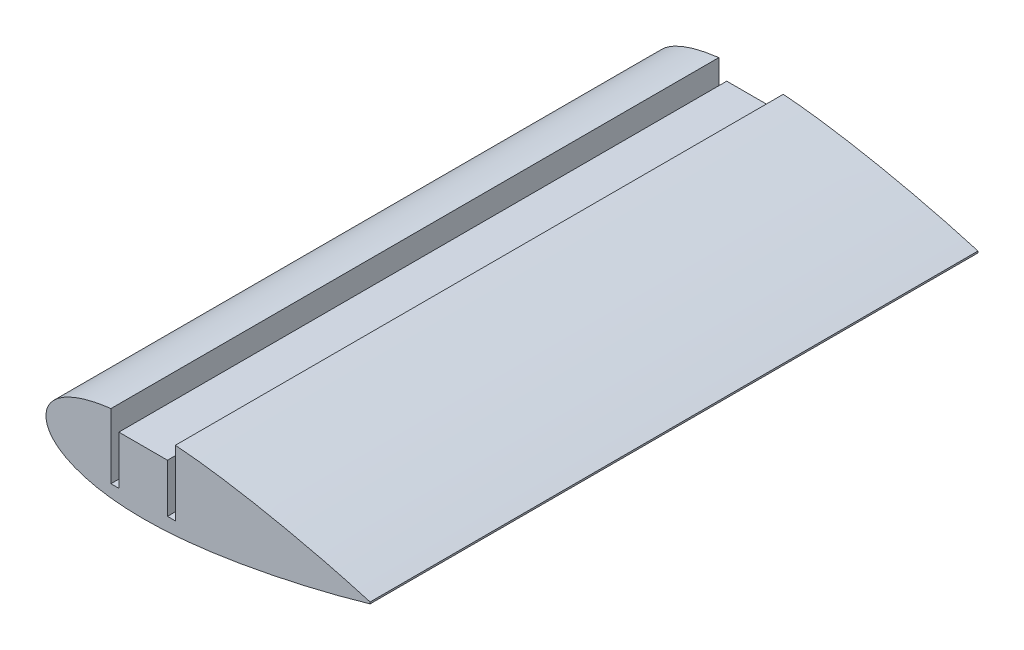
SolidWorks part; units mm, degrees
ref_plane "Спереди" through (0, 0, 0) normal (0, 0, 1) x (1, 0, 0)
ref_plane "Сверху" through (0, 0, 0) normal (0, 1, 0) x (1, 0, 0)
ref_plane "Справа" through (0, 0, 0) normal (1, 0, 0) x (0, 0, -1)
other "Configuration Table"
curve "Curve1"
  spline degree 3 poles (1, 0.0026, 0) (0.9995, 0.0028, 0) (0.9974, 0.0034, 0) (0.9928, 0.0047, 0) (0.9852, 0.0069, 0) (0.9746, 0.01, 0) (0.961, 0.0138, 0) (0.9446, 0.0183, 0) (0.9255, 0.0235, 0) (0.9037, 0.0292, 0) (0.8794, 0.0355, 0) (0.8529, 0.0421, 0) (0.8241, 0.0491, 0) (0.7933, 0.0562, 0) (0.7607, 0.0635, 0) (0.7266, 0.0709, 0) (0.691, 0.0782, 0) (0.6542, 0.0854, 0) (0.6165, 0.0923, 0) (0.5781, 0.0988, 0) (0.5392, 0.1049, 0) (0.5, 0.1104, 0) (0.4609, 0.1152, 0) (0.422, 0.1192, 0) (0.3836, 0.1222, 0) (0.3458, 0.1243, 0) (0.3091, 0.1252, 0) (0.2735, 0.1249, 0) (0.2392, 0.1234, 0) (0.2066, 0.1205, 0) (0.1758, 0.1164, 0) (0.147, 0.111, 0) (0.1203, 0.1043, 0) (0.096, 0.0965, 0) (0.0741, 0.0875, 0) (0.0549, 0.0774, 0) (0.0383, 0.0665, 0) (0.0245, 0.0546, 0) (0.0137, 0.042, 0) (0.0058, 0.0286, 0) (0.001, 0.0145, 0) (-0.0005, 0, 0) (0.001, -0.0145, 0) (0.0058, -0.0286, 0) (0.0137, -0.042, 0) (0.0245, -0.0546, 0) (0.0383, -0.0665, 0) (0.0549, -0.0774, 0) (0.0741, -0.0875, 0) (0.096, -0.0965, 0) (0.1203, -0.1043, 0) (0.147, -0.111, 0) (0.1758, -0.1164, 0) (0.2066, -0.1205, 0) (0.2392, -0.1234, 0) (0.2735, -0.1249, 0) (0.3091, -0.1252, 0) (0.3458, -0.1243, 0) (0.3836, -0.1222, 0) (0.422, -0.1192, 0) (0.4609, -0.1152, 0) (0.5, -0.1104, 0) (0.5392, -0.1049, 0) (0.5781, -0.0988, 0) (0.6165, -0.0923, 0) (0.6542, -0.0854, 0) (0.691, -0.0782, 0) (0.7266, -0.0709, 0) (0.7607, -0.0635, 0) (0.7933, -0.0562, 0) (0.8241, -0.0491, 0) (0.8529, -0.0421, 0) (0.8794, -0.0355, 0) (0.9037, -0.0292, 0) (0.9255, -0.0235, 0) (0.9446, -0.0183, 0) (0.961, -0.0138, 0) (0.9746, -0.01, 0) (0.9852, -0.0069, 0) (0.9928, -0.0047, 0) (0.9974, -0.0034, 0) (0.9995, -0.0028, 0) (1, -0.0026, 0) knots 0 0 0 0 0.000754 0.003013 0.006759 0.011967 0.018601 0.026614 0.035953 0.046555 0.058348 0.071256 0.085193 0.100071 0.115793 0.132259 0.149363 0.166997 0.185048 0.203403 0.221946 0.240561 0.259134 0.27755 0.295701 0.313483 0.330797 0.347552 0.363666 0.379065 0.393686 0.407475 0.420392 0.432406 0.443503 0.453686 0.462984 0.471456 0.479204 0.486388 0.493229 0.5 0.506771 0.513612 0.520796 0.528544 0.537016 0.546314 0.556497 0.567594 0.579608 0.592525 0.606314 0.620935 0.636334 0.652448 0.669203 0.686517 0.704299 0.72245 0.740866 0.759439 0.778054 0.796597 0.814952 0.833003 0.850637 0.867741 0.884207 0.899929 0.914807 0.928744 0.941652 0.953445 0.964047 0.973386 0.981399 0.988033 0.993241 0.996987 0.999246 1 1 1 1
sketch "Sketch2" plane through (0, 0, 0) normal (0, 0, 1) x (1, 0, 0)
  line L0 (55.999, 0.2099) -> (55.999, -0.2099) construction
  line L1 (55.999, 0) -> (-23.9777, 0) construction
  line L2 (-23.9777, 0) -> (-23.9777, 20.1567) construction
  line L3 (-7.5754, 10) -> (21.8908, 10) construction
  line L4 (55.999, 0.2099) -> (55.999, -0.2099)
  line L5 (0, 10) -> (0, -10) construction
  line L6 (55.999, -0.2099) -> (55.999, 14.9208) construction
  spline S1 degree 3 poles (55.999, 0.2099) (53.4639, 0.9505) (48.8039, 2.2339) (42.4289, 3.8199) (36.7434, 5.1209) (31.1997, 6.2872) (25.2824, 7.4075) (20.1765, 8.2452) (14.9796, 8.9749) (10.8215, 9.4486) (6.6974, 9.777) (3.6807, 9.9396) (0.7396, 10.0127) (-2.1078, 9.99) (-4.8439, 9.867) (-7.4522, 9.6409) (-9.9165, 9.3106) (-12.2218, 8.8772) (-14.354, 8.3437) (-16.3004, 7.7143) (-18.0494, 6.9954) (-19.5906, 6.1934) (-20.9154, 5.3156) (-22.0159, 4.3681) (-22.8849, 3.3565) (-23.5145, 2.285) (-23.8954, 1.1588) (-24.0187, 0) (-23.8954, -1.1588) (-23.5145, -2.285) (-22.8849, -3.3565) (-22.0159, -4.3681) (-20.9154, -5.3156) (-19.5906, -6.1934) (-18.0494, -6.9954) (-16.3004, -7.7143) (-14.354, -8.3437) (-12.2218, -8.8772) (-9.9165, -9.3106) (-7.4522, -9.6409) (-4.8439, -9.867) (-2.1078, -9.99) (0.7396, -10.0127) (3.6807, -9.9396) (7.7407, -9.7208) (12.9128, -9.2413) (19.1367, -8.4158) (25.2824, -7.4074) (31.1998, -6.2873) (37.5172, -4.9581) (44.7426, -3.2759) (51.0576, -1.6263) (54.945, -0.5178) (55.9579, -0.2219) (55.999, -0.2099) knots 0 0 0 0 0.046555 0.085193 0.115793 0.149363 0.185048 0.221946 0.240561 0.27755 0.295701 0.313483 0.330797 0.347552 0.363666 0.379065 0.393686 0.407475 0.420392 0.432406 0.443503 0.453686 0.462984 0.471456 0.479204 0.486388 0.493229 0.5 0.506771 0.513612 0.520796 0.528544 0.537016 0.546314 0.556497 0.567594 0.579608 0.592525 0.606314 0.620935 0.636334 0.652448 0.669203 0.686517 0.704299 0.740866 0.778054 0.814952 0.850637 0.884207 0.928744 0.981399 0.999246 1 1 1 1
  point P11 (0, 0)
  dimension "D1" = 20
extrude "Boss-Extrude1" add sketch "Sketch2" along normal blind 150
sketch "Sketch3" plane through (0, 0, 0) normal (0, 0, -1) x (-1, 0, 0)
  line L0 (6, -6.5) -> (7.95, -6.5)
  line L2 (-6, -6.5) -> (-6, 5.5)
  line L3 (-6, 5.5) -> (6, 5.5)
  line L4 (6, -6.5) -> (6, 5.5)
  line L5 (-6, -6.5) -> (6, 5.5) construction
  line L6 (-6, 5.5) -> (6, -6.5) construction
  line L7 (7.95, -6.5) -> (7.95, 9.5637)
  line L8 (-6, -6.5) -> (-7.95, -6.5)
  line L9 (-7.95, -6.5) -> (-7.95, 9.6738)
  line L10 (-11.2468, 10) -> (11.5184, 10) construction
  line L11 (0, 0) -> (0, 6.0357) construction
  line L12 (-7.95, -6.5) -> (7.95, -6.5) construction
  spline S0 degree 3 poles (275.2851, -1947.3186) (-351.5026, -245.2226) (-218.8463, -40.0718) (-42.4289, 3.8199) (-36.7434, 5.1209) (-31.1997, 6.2872) (-25.2824, 7.4075) (-20.1765, 8.2452) (-14.9796, 8.9749) (-10.8215, 9.4486) (-6.6974, 9.777) (-3.6807, 9.9396) (-0.7396, 10.0127) (2.1078, 9.99) (4.8439, 9.867) (7.4522, 9.6409) (9.9165, 9.3106) (12.2218, 8.8772) (14.354, 8.3437) (16.3004, 7.7143) (18.0494, 6.9954) (19.5906, 6.1934) (20.9154, 5.3156) (22.0159, 4.3681) (22.8849, 3.3565) (23.5145, 2.285) (23.8954, 1.1588) (24.0187, 0) (23.8954, -1.1588) (23.5145, -2.285) (22.8849, -3.3565) (22.0159, -4.3681) (20.9154, -5.3156) (19.5906, -6.1934) (18.0494, -6.9954) (16.3004, -7.7143) (14.354, -8.3437) (12.2218, -8.8772) (9.9165, -9.3106) (7.4522, -9.6409) (4.8439, -9.867) (2.1078, -9.99) (-0.7396, -10.0127) (-3.6807, -9.9396) (-7.7407, -9.7208) (-12.9128, -9.2413) (-19.1367, -8.4158) (-25.2824, -7.4074) (-31.1998, -6.2873) (-37.5172, -4.9581) (-44.7426, -3.2759) (-51.0576, -1.6263) (-78.1348, 6.0944) (-101.2564, 16.704) (-685.5525, -1897.6172) knots -3.088599 -3.088599 -3.088599 -3.088599 0.046555 0.085193 0.115793 0.149363 0.185048 0.221946 0.240561 0.27755 0.295701 0.313483 0.330797 0.347552 0.363666 0.379065 0.393686 0.407475 0.420392 0.432406 0.443503 0.453686 0.462984 0.471456 0.479204 0.486388 0.493229 0.5 0.506771 0.513612 0.520796 0.528544 0.537016 0.546314 0.556497 0.567594 0.579608 0.592525 0.606314 0.620935 0.636334 0.652448 0.669203 0.686517 0.704299 0.740866 0.778054 0.814952 0.850637 0.884207 0.928744 0.981399 0.999246 1.425061 1.425061 1.425061 1.425061 only from (-55.999, 0.2099) to (-55.999, -0.2099) construction
  spline S1 degree 3 poles (-7.95, 9.6738) (-7.5253, 9.7065) (-6.0943, 9.8095) (-3.6807, 9.9396) (-0.7396, 10.0127) (2.1078, 9.99) (4.8439, 9.867) (6.7781, 9.6993) (7.7981, 9.5819) (7.95, 9.5637) knots 0.288193 0.288193 0.288193 0.288193 0.295701 0.313483 0.330797 0.347552 0.363666 0.379065 0.381762 0.381762 0.381762 0.381762
  point P0 (0, -0.5)
  point P13 (-6.975, -6.5)
  dimension "D1" = 12
  dimension "D2" = 12
  dimension "D3" = 1.95
  dimension "D4" = 1.95
  dimension "D5" = 16.5
extrude "Cut-Extrude1" cut sketch "Sketch3" against normal up to next
